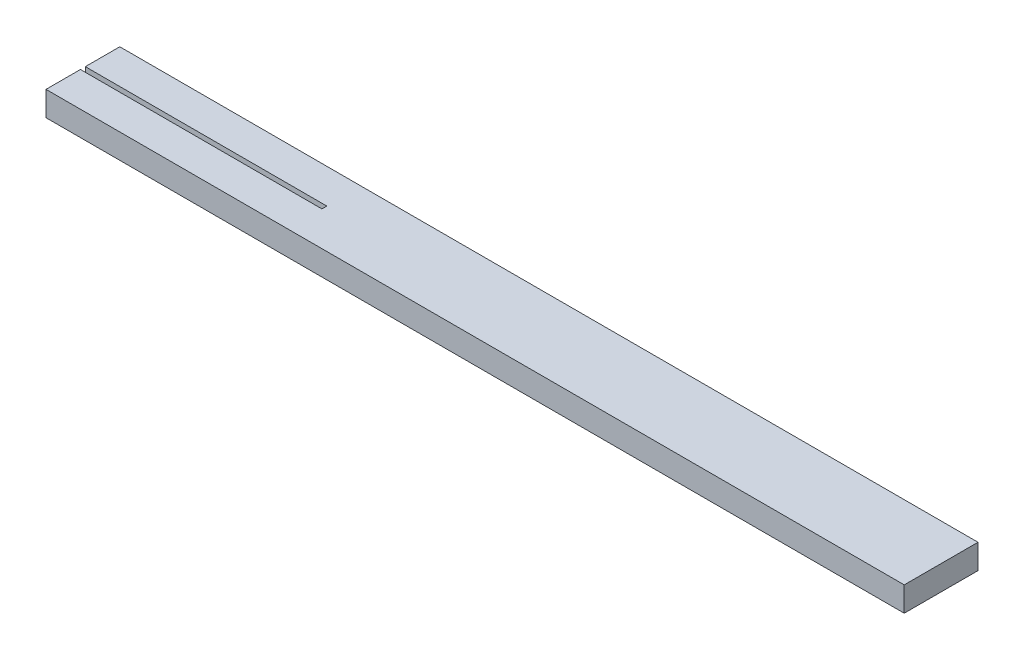
SolidWorks part; units mm, degrees
ref_plane "前视基准面" through (0, 0, 0) normal (0, 0, 1) x (1, 0, 0)
ref_plane "上视基准面" through (0, 0, 0) normal (0, 1, 0) x (1, 0, 0)
ref_plane "右视基准面" through (0, 0, 0) normal (1, 0, 0) x (0, 0, -1)
ref_plane "base plane" through (0, 1, 0) normal (0, 1, 0) x (1, 0, 0)
sketch "草图1" plane through (0, 1, 0) normal (0, 1, 0) x (1, 0, 0)
  line L0 (-7.2192, 5.813) -> (-7.2192, 5.613)
  line L1 (-7.2192, 5.613) -> (-17.0392, 5.613)
  line L2 (-17.0392, 5.613) -> (-17.0392, 4.213)
  line L3 (-17.0392, 4.213) -> (-4.1892, 4.213)
  line L8 (17.8608, 4.213) -> (17.8608, 7.213)
  line L14 (-17.0392, 7.213) -> (-17.0392, 5.813)
  line L15 (-17.0392, 5.813) -> (-7.2192, 5.813)
  line L43 (-2.8537, 4.213) -> (17.8608, 4.213)
  line L44 (17.8608, 7.213) -> (-4.9478, 7.213)
  line L45 (-5.0892, 7.213) -> (-17.0392, 7.213)
  line L46 (-4.9478, 7.213) -> (-5.0892, 7.213)
  line L47 (-4.1892, 4.213) -> (-2.8537, 4.213)
extrude "凸台-拉伸1" add sketch "草图1" against normal blind 1
sketch "草图4" plane through (0, 1, 0) normal (0, 1, 0) x (1, 0, 0)
  line L0 (-7.2192, 5.713) -> (-5.2192, 5.713)
  line L1 (-7.2192, 5.813) -> (-7.2192, 5.613) construction
  line L7 (-17.0392, 4.213) -> (17.8608, 4.213) construction
  line L10 (-5.2192, 4.213) -> (-4.2192, 4.213)
  line L11 (-4.2192, 4.213) -> (-3.2192, 4.213)
  line L12 (-2.2192, 5.213) -> (-2.2192, 6.213)
  line L13 (-2.2192, 6.213) -> (-2.2192, 7.213)
  line L14 (-2.2192, 5.713) -> (-0.2192, 5.713)
  line L15 (-2.2192, 4.213) -> (-3.2192, 4.213)
  line L16 (-2.2192, 4.213) -> (-2.2192, 5.213)
  line L17 (17.8608, 7.213) -> (-17.0392, 7.213) construction
  line L18 (-3.2192, 5.213) -> (-3.2192, 6.213)
  line L19 (-3.2192, 6.213) -> (-3.2192, 7.213)
  line L20 (-3.2192, 4.213) -> (-3.2192, 5.213)
  line L21 (-4.2192, 5.213) -> (-4.2192, 6.213)
  line L22 (-4.2192, 6.213) -> (-4.2192, 7.213)
  line L23 (-4.2192, 4.213) -> (-4.2192, 5.213)
  line L24 (-5.2192, 5.213) -> (-5.2192, 6.213)
  line L25 (-5.2192, 6.213) -> (-5.2192, 7.213)
  line L26 (-5.2192, 4.213) -> (-5.2192, 5.213)
  line L27 (-5.2192, 5.213) -> (-4.2192, 5.213)
  line L28 (-4.2192, 5.213) -> (-3.2192, 5.213)
  line L29 (-2.2192, 5.213) -> (-3.2192, 5.213)
  line L30 (-5.2192, 6.213) -> (-4.2192, 6.213)
  line L31 (-4.2192, 6.213) -> (-3.2192, 6.213)
  line L32 (-2.2192, 6.213) -> (-3.2192, 6.213)
  line L33 (-5.2192, 7.213) -> (-4.2192, 7.213)
  line L34 (-4.2192, 7.213) -> (-3.2192, 7.213)
  line L35 (-2.2192, 7.213) -> (-3.2192, 7.213)
  dimension "D1" = 4
